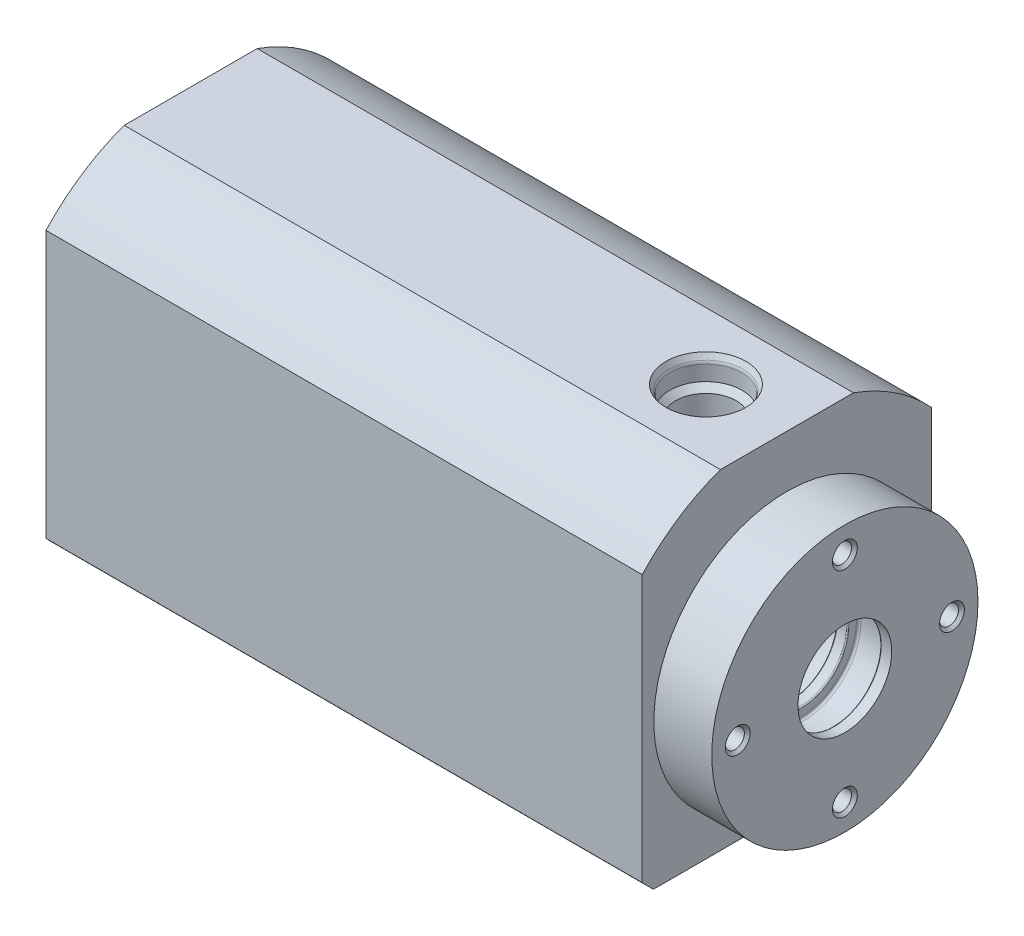
SolidWorks part; units mm, degrees
material "Сплав 3М ОСТ 1.92077-91"
ref_plane "Plane1" through (0, 0, 0) normal (0, 0, 1) x (1, 0, 0)
ref_plane "Plane2" through (0, 0, 0) normal (0, 1, 0) x (1, 0, 0)
ref_plane "Plane3" through (0, 0, 0) normal (1, 0, 0) x (0, 0, -1)
sketch "Эскиз1" plane through (0, 0, 0) normal (0, 0, 1) x (1, 0, 0)
  line L0 (0, 0) -> (-43.5313, 0) construction
  line L1 (0, 34) -> (0, 16)
  line L2 (0, 16) -> (85, 16)
  line L3 (85, 16) -> (85, 8.1)
  line L4 (85, 8.1) -> (99.9, 8.1)
  line L5 (103, 23) -> (103, 34)
  line L6 (103, 34) -> (0, 34)
  line L7 (103, 23) -> (113, 23)
  line L8 (113, 23) -> (113, 8.1)
  line L9 (111, 8.1) -> (111, 10)
  line L10 (111, 10) -> (105.4, 10)
  line L11 (105.4, 10) -> (105.4, 8.1)
  line L12 (111, 8.1) -> (113, 8.1)
  line L13 (103.4, 8.1) -> (103.4, 9.9)
  line L14 (103.4, 9.9) -> (99.9, 9.9)
  line L15 (99.9, 9.9) -> (99.9, 8.1)
  line L16 (103.4, 8.1) -> (105.4, 8.1)
  dimension "D1" = 32
  dimension "D2" = 68
  dimension "D3" = 16.2
  dimension "D4" = 85
  dimension "D5" = 18
  dimension "D6" = 46
  dimension "D7" = 10
  dimension "D8" = 5.6
  dimension "D9" = 20
  dimension "D10" = 2
  dimension "D11" = 3.5
  dimension "D12" = 19.8
  dimension "D13" = 2
revolve "Повернуть1" add sketch "Эскиз1" angle 360 about L0
sketch "Эскиз2" plane through (0, 0, 0) normal (-1, 0, 0) x (0, 0, 1)
  line L0 (-11.4891, 32) -> (11.4891, 32)
  line L1 (-25, -25) -> (25, -25)
  line L2 (-25, -25) -> (-25, 23.0434)
  line L3 (0, -25) -> (0, 0) construction
  line L4 (25, -25) -> (25, 23.0434)
  circle A0 centre (0, 0) radius 34 construction
  arc A1 (-11.4891, 32) -> (-25, 23.0434) centre (0, 0) ccw
  arc A3 (25, 23.0434) -> (11.4891, 32) centre (0, 0) ccw
  point P0 (0, 0)
  dimension "D2" = 57
  dimension "D3" = 25
  dimension "D4" = 50
extrude "Вырез-Вытянуть1" cut sketch "Эскиз2" against normal through all flip side to cut
chamfer "Фаска1" distance 1.3 angle 75 1 edges at (0, 0, -16)
fillet "Скругление1" radius 2 1 edges at (4.8517, 0, 16)
fillet "Скругление2" radius 1 1 edges at (0, 0, 17.3)
hole_wizard "Отверстие обработанное метчиком M64" positions "Эскиз6" profile "Эскиз5" tap size "M6" standard "ISO"
sketch "Эскиз6" plane through (0, 0, 0) normal (-1, 0, 0) x (0, 0, 1)
  line L0 (0, 0) -> (16.9706, 16.9706) construction
  line L1 (0, 0) -> (0, 6.8601) construction
  point P0 (16.9706, 16.9706)
  dimension "D1" = 45
  dimension "D2" = 24
sketch "Эскиз5" plane through (0, 16.9706, 16.9706) normal (0, 1, 0) x (0, 0, 1)
  line L0 (0, 0) -> (0, 17.2871)
  line L1 (0, 17.2871) -> (2.475, 15.8)
  line L2 (2.475, 15.8) -> (2.475, 1)
  line L3 (2.475, 1) -> (3.475, 0)
  line L5 (3.475, 0) -> (0, 0)
  line L6 (-2.475, 1) -> (-3.475, 0) construction
  line L10 (0, 17.2871) -> (-2.475, 15.8) construction
  line L11 (0, -6.35) -> (0, 107.95) construction
  dimension "Диаметр сверла" = 4.95
  dimension "Глубина сверла" = 15.8
  dimension "Диаметр передней зенковки" = 6.95
  dimension "Угол передней зенковки" = 90
  dimension "Угол заточки сверла" = 118
cosmetic thread "Отверстие резьбы1" parameters "D1"=12, "D2"=6
pattern_circular "Круговой массив1" count 4 over 360 about axis through (0, 0, 0) along (1, 0, 0) of "Отверстие обработанное метчиком M64"
hole_wizard "Отверстие обработанное метчиком M63" positions "Эскиз8" profile "Эскиз7" tap size "M6" standard "ISO"
sketch "Эскиз8" plane through (0, -25, 0) normal (0, -1, 0) x (-1, 0, 0)
  line L0 (-95, 19) -> (-95, -19) construction
  line L1 (-95, -19) -> (-43, -19) construction
  line L2 (-43, -19) -> (-43, 19) construction
  line L3 (-43, 19) -> (-95, 19) construction
  line L4 (-43, 0) -> (0, 0) construction
  line L5 (-103, -23.0434) -> (-103, 23.0434) construction
  point P0 (-95, -19)
  point P3 (-95, 19)
  point P5 (-43, 19)
  point P7 (-43, -19)
  dimension "D1" = 38
  dimension "D2" = 8
  dimension "D3" = 52
sketch "Эскиз7" plane through (95, -25, 19) normal (1, 0, 0) x (0, 0, -1)
  line L0 (0, 0) -> (0, 20.4871)
  line L1 (0, 20.4871) -> (2.475, 19)
  line L2 (2.475, 19) -> (2.475, 1)
  line L3 (2.475, 1) -> (3.475, 0)
  line L5 (3.475, 0) -> (0, 0)
  line L6 (-2.475, 1) -> (-3.475, 0) construction
  line L10 (0, 20.4871) -> (-2.475, 19) construction
  line L11 (0, -6.35) -> (0, 107.95) construction
  dimension "Диаметр сверла" = 4.95
  dimension "Глубина сверла" = 19
  dimension "Диаметр передней зенковки" = 6.95
  dimension "Угол передней зенковки" = 90
  dimension "Угол заточки сверла" = 118
cosmetic thread "Отверстие резьбы2" parameters "D1"=14, "D2"=6
cosmetic thread "Отверстие резьбы3" parameters "D1"=14, "D2"=6
cosmetic thread "Отверстие резьбы4" parameters "D1"=14, "D2"=6
cosmetic thread "Отверстие резьбы5" parameters "D1"=14, "D2"=6
sketch "Sketch4" plane through (67.2042, 32, -2.2917) normal (0, 1, 0) x (-1, 0, 0)
  line L0 (-21.7958, 2.2917) -> (-21.7958, 4.4017) construction
  line L1 (-21.7958, 2.2917) -> (-16.6858, 2.2917) construction
  line L3 (-35.7958, 13.7808) -> (-35.7958, -9.1975) construction
  point P0 (-21.7958, 2.2917)
  point P3 (-16.6858, 2.2917)
  dimension "D1" = 5.11
  dimension "D2" = 2.11
  dimension "D3" = 90
  dimension "D4" = 14
ref_plane "Plane4_для_эскиза_отверстия" through (89, 32, 0) normal (0, 0, 1) x (1, 0, 0)
ref_plane "Plane5_начало_резьбы" through (0, 32, 0) normal (0, -1, 0) x (-1, 0, 0)
sketch "Sketch2" plane through (89, 32, 0) normal (0, 0, 1) x (1, 0, 0)
  line L0 (0, 0) -> (0, -22.1034)
  line L1 (-6.9, 0) -> (-6.384, -0.8938)
  line L2 (6.384, -0.8938) -> (6.9, 0) construction
  line L3 (-6.25, -1.3938) -> (-6.25, -4)
  line L4 (-6.25, -4) -> (-5.215, -5.035)
  line L5 (-5.215, -5.035) -> (-5.215, -13)
  line L6 (-5.165, -19) -> (0, -22.1034)
  line L7 (-6.9, 0) -> (0, 0)
  line L8 (0, 0) -> (0, 3.9197) construction
  line L9 (-5.215, -13) -> (-5.165, -13)
  line L11 (6.25, -1.3938) -> (6.25, -4) construction
  line L12 (-5.165, -13) -> (-5.165, -19)
  line L13 (6.25, -4) -> (5.215, -5.035) construction
  line L14 (0, -22.1034) -> (5.165, -19) construction
  arc A0 (-6.384, -0.8938) -> (-6.25, -1.3938) centre (-7.25, -1.3938) cw
  arc A1 (6.25, -1.3938) -> (6.384, -0.8938) centre (7.25, -1.3938) cw construction
  point P2 (-6, -13)
  point P19 (-6.9, 0)
  dimension "D9" = 1
  dimension "D10" = 1
  dimension "D1_уплотнение" = 12.5
  dimension "D2_фаска" = 13.8
  dimension "D3_под_резьбу" = 10.43
  dimension "D4_глубина_сверления" = 19
  dimension "D5" = 4
  dimension "D6" = 60
  dimension "D7" = 90
  dimension "D8" = 118
  dimension "D11" = 0.05
  dimension "D1_диаметр" = 12
  dimension "D2_глубина_резьбы" = 13
revolve "Cut-Revolve1" cut sketch "Sketch2" angle 360 about L8
cosmetic thread "Условное изображение резьбы1" parameters "D1_диаметр"=12
other "Отв_ГОСТ_19529-74 - <1>"
sketch "Эскиз11" plane through (85, 0, 0) normal (-1, 0, 0) x (0, 0, 1)
  circle A0 centre (0, 13.5) radius 2
  dimension "D1" = 4
  dimension "D2" = 13.5
extrude "Вырез-Вытянуть2" [suppressed] cut sketch "Эскиз11" against normal up to next
hole_wizard "Отверстие обработанное метчиком M42" positions "Эскиз13" profile "Эскиз12" tap size "M4" standard "ISO"
sketch "Эскиз13" plane through (113, 0, 0) normal (1, 0, 0) x (0, 0, -1)
  point P0 (0, 18.5)
  dimension "D1" = 18.5
sketch "Эскиз12" plane through (113, 18.5, 0) normal (0, 1, 0) x (0, 0, -1)
  line L0 (0, 0) -> (0, 12.4914)
  line L1 (0, 12.4914) -> (1.65, 11.5)
  line L2 (1.65, 11.5) -> (1.65, 0.5)
  line L3 (1.65, 0.5) -> (2.15, 0)
  line L5 (2.15, 0) -> (0, 0)
  line L6 (-1.65, 0.5) -> (-2.15, 0) construction
  line L10 (0, 12.4914) -> (-1.65, 11.5) construction
  line L11 (0, -6.35) -> (0, 107.95) construction
  dimension "Диаметр сверла" = 3.3
  dimension "Глубина сверла" = 11.5
  dimension "Диаметр передней зенковки" = 4.3
  dimension "Угол передней зенковки" = 90
  dimension "Угол заточки сверла" = 118
cosmetic thread "Отверстие резьбы6" parameters "D1"=8, "D2"=4
pattern_circular "Круговой массив2" count 4 over 360 about axis through (0, 0, 0) along (1, 0, 0) of "Отверстие обработанное метчиком M42"
chamfer "Фаска2" distance 1 angle 45 1 edges at (85, 0, -8.1)
fillet "Скругление3" radius 0.4 4 edges at (99.9, 0, -9.9) (103.4, 0, -9.9) (105.4, 0, -10) (111, 0, -10)
fillet "Скругление4" radius 0.2 4 edges at (111, 0, -8.1) (105.4, 0, -8.1) (103.4, 0, -8.1) (99.9, 0, -8.1)
sketch "Эскиз14" plane through (0, 0, 0) normal (0, 0, 1) x (1, 0, 0)
  line L0 (0, 0) -> (-10.959, 0) construction
  line L2 (79, 19) -> (51, 19)
  line L3 (79, 19) -> (79, 40)
  line L4 (79, 40) -> (51, 40)
  line L5 (51, 19) -> (51, 40)
  line L6 (103, -23) -> (103, 23) construction
  dimension "D1" = 24
  dimension "D2" = 28
  dimension "D3" = 38
  dimension "D4" = 80
revolve "Вырез-Повернуть2" [suppressed] cut sketch "Эскиз14" angle 360 about L0
